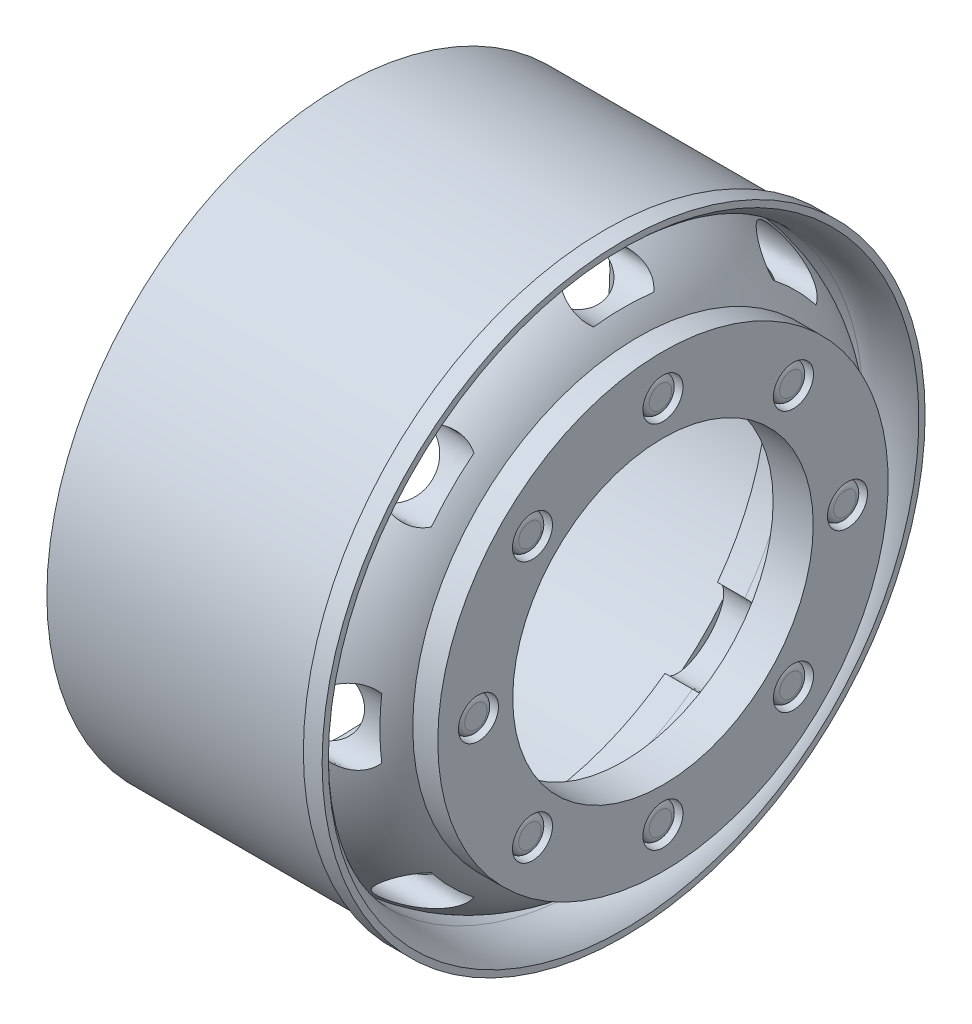
SolidWorks part; units mm, degrees
ref_plane "Front Plane" through (0, 0, 0) normal (0, 0, 1) x (1, 0, 0)
ref_plane "Top Plane" through (0, 0, 0) normal (0, 1, 0) x (1, 0, 0)
ref_plane "Right Plane" through (0, 0, 0) normal (1, 0, 0) x (0, 0, -1)
sketch "Sketch1" plane through (0, 0, 0) normal (0, 0, 1) x (1, 0, 0)
  line L0 (-25, 0) -> (25, 0) construction
  line L1 (0, 36.6286) -> (0, -30.4082) construction
  line L2 (-10, 23.5) -> (11.1, 23.5)
  line L3 (11.1, 23.5) -> (11.1, 24.1)
  line L4 (11.1, 24.1) -> (12.6, 24.1)
  line L5 (12.6, 24.1) -> (12.6, 23.6)
  line L9 (-10, 21.5) -> (-10, 23.5)
  line L27 (9.4257, 22.3) -> (6, 22.3)
  line L36 (13.7458, 18) -> (15.7458, 18)
  line L43 (-10, 21.5) -> (3.8066, 21.5)
  line L44 (6, 20.3) -> (3.8066, 20.3)
  line L45 (3.8066, 20.3) -> (3.8066, 21.5)
  line L47 (12.542, 16) -> (12.542, 8.4837)
  line L48 (-10, 21.5) -> (11.1, 21.5) construction
  line L49 (15.7458, 18) -> (15.7458, 0) construction
  line L51 (13.7458, 16) -> (13.7458, 0) construction
  line L52 (12.542, 8.4837) -> (15.7458, 8.4837)
  line L53 (15.7458, 8.4837) -> (15.7458, 18)
  line L55 (12.542, 16) -> (13.7458, 16) construction
  arc A1 (12.6, 23.6) -> (9.4257, 22.3) centre (9.6236, 26.3422) cw
  arc A4 (6, 22.3) -> (13.7458, 18) centre (6, 13.1735) cw
  arc A5 (6, 20.3) -> (12.542, 16) centre (6, 13.1735) cw
  point P13 (12.9671, 14)
  point P21 (16.5518, 14)
  point P24 (12.9671, 11)
  point P27 (16.5518, 11)
  dimension "D1" = 50
  dimension "D2" = 25
  dimension "D3" = 2
  dimension "D4" = 21.1
  dimension "D5" = 48.2
  dimension "D6" = 0.5
  dimension "D7" = 1.5
  dimension "D9" = 2
  dimension "D10" = 2
  dimension "D11" = 47
revolve "Revolve1" add sketch "Sketch1" angle 360 about L0
sketch "Sketch3" plane through (12.6, 0, 0) normal (1, 0, 0) x (0, 0, -1)
  line L0 (0, 23.6) -> (0, -24.1) construction
  line L1 (-24.1, 0) -> (24.1, 0) construction
  circle A0 centre (0, 0) radius 23.6 construction
  circle A1 centre (0, 0) radius 24.1 construction
  ellipse E0 centre (0, 20.3231) end of major axis (3, 20.3231) minor radius 1.6667
  dimension "D1" = 6
extrude "Cut-Extrude2" cut sketch "Sketch3" against normal up to surface (8.7934 mm away) up to face at (3.8066, 0, 20.3)
pattern_circular "CirPattern1" count 8 over 360 about axis through (15.7458, 0, 0) along (-1, 0, 0) of "Cut-Extrude2"
sketch "Sketch5" plane through (15.7458, 0, 0) normal (1, 0, 0) x (0, 0, -1)
  circle A0 centre (0, 0) radius 14.75 construction
  circle A1 centre (0, 14.75) radius 1.6
  circle A2 centre (10.4298, 10.4298) radius 1.6
  circle A3 centre (14.75, 0) radius 1.6
  circle A4 centre (10.4298, -10.4298) radius 1.6
  circle A5 centre (0, -14.75) radius 1.6
  circle A6 centre (-10.4298, -10.4298) radius 1.6
  circle A7 centre (-14.75, 0) radius 1.6
  circle A8 centre (-10.4298, 10.4298) radius 1.6
  point P22 (0, 0)
  dimension "D1" = 29.5
  dimension "D2" = 3.2
  dimension "D3" = 8
extrude "Cut-Extrude3" cut sketch "Sketch5" against normal offset from surface (1.7038 mm away) 1.5 up to face at (12.542, 0, 8.4837)
sketch "Sketch6" plane through (14.042, 0, 0) normal (1, 0, 0) x (0, 0, -1)
  line L0 (-14.75, 1.6) -> (-14.75, -1.6) construction
  line L1 (-16.35, 0) -> (-13.15, 0) construction
  circle A0 centre (-14.75, 0) radius 1.6 construction
  circle A1 centre (-14.75, 0) radius 1.6 construction
  circle A2 centre (-14.75, 0) radius 1.4
  circle A3 centre (-10.4298, 10.4298) radius 1.4
  circle A4 centre (0, 14.75) radius 1.4
  circle A5 centre (10.4298, 10.4298) radius 1.4
  circle A6 centre (14.75, 0) radius 1.4
  circle A7 centre (10.4298, -10.4298) radius 1.4
  circle A8 centre (0, -14.75) radius 1.4
  circle A9 centre (-10.4298, -10.4298) radius 1.4
  point P28 (0, 0)
  dimension "D1" = 2.8
  dimension "D2" = 8
extrude "Boss-Extrude1" add sketch "Sketch6" along normal blind 1.5
fillet "Fillet1" radius 0.5 8 edges at (15.542, 0, -16.15) (15.542, -10.4298, -11.8298) (15.542, -14.75, -1.4) (15.542, -10.4298, 9.0298) (15.542, 0, 13.35) (15.542, 10.4298, 9.0298) (15.542, 14.75, -1.4) (15.542, 10.4298, -11.8298)
sketch "Sketch7" plane through (15.7458, 0, 0) normal (1, 0, 0) x (0, 0, -1)
  circle A0 centre (0, 0) radius 12.0088
extrude "Cut-Extrude4" cut sketch "Sketch7" against normal through all
